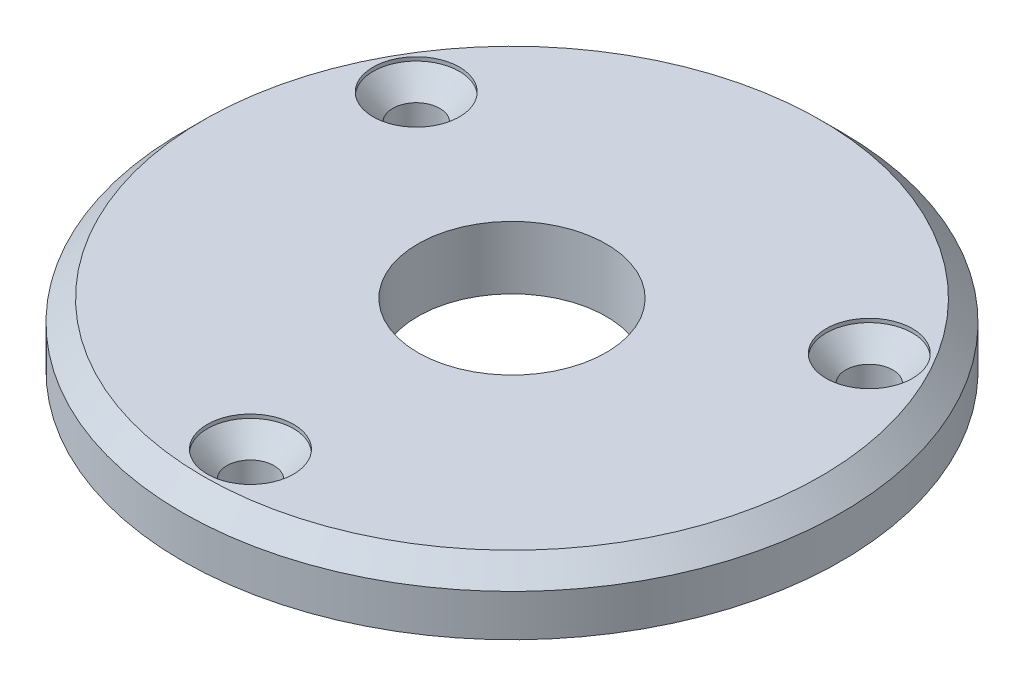
SolidWorks part; units mm, degrees
ref_plane "Alzado" through (0, 0, 0) normal (0, 0, 1) x (1, 0, 0)
ref_plane "Planta" through (0, 0, 0) normal (0, 1, 0) x (1, 0, 0)
ref_plane "Vista lateral" through (0, 0, 0) normal (1, 0, 0) x (0, 0, -1)
sketch "Croquis1" plane through (0, 0, 0) normal (0, 1, 0) x (1, 0, 0)
  circle A0 centre (0, 0) radius 31.5
  circle A1 centre (0, 0) radius 9
  dimension "D1" = 63
  dimension "D2" = 18
extrude "Saliente-Extruir1" add sketch "Croquis1" along normal blind 6
chamfer "Chaflán1" distance 2 angle 45 1 edges at (0, 6, 31.5)
sketch "Croquis2" plane through (0, 0, 0) normal (1, 0, 0) x (0, 0, -1)
  line L0 (-25, -2.3159) -> (-25, 8.5175) construction
  line L1 (0, -3.5756) -> (0, 10.6841) construction
  line L2 (-25, 0) -> (-25, 6)
  line L3 (-31.5, 0) -> (31.5, 0) construction
  line L4 (-25, 6) -> (-20.875, 6)
  line L5 (-20.875, 5.64) -> (-22.75, 3.52)
  line L6 (-22.75, 3.52) -> (-22.75, 0)
  line L7 (-22.75, 0) -> (-25, 0)
  line L8 (29.5, 6) -> (-29.5, 6) construction
  line L9 (-20.875, 6) -> (-20.875, 5.64)
  dimension "D1" = 25
  dimension "D2" = 8.25
  dimension "D3" = 2.48
  dimension "D4" = 4.5
  dimension "D5" = 0.36
revolve "Cortar-Revolución1" cut sketch "Croquis2" angle 360 about L2
pattern_circular "MatrizC1" count 3 over 360 about axis through (0, 0, 0) along (0, 1, 0) of "Cortar-Revolución1"
